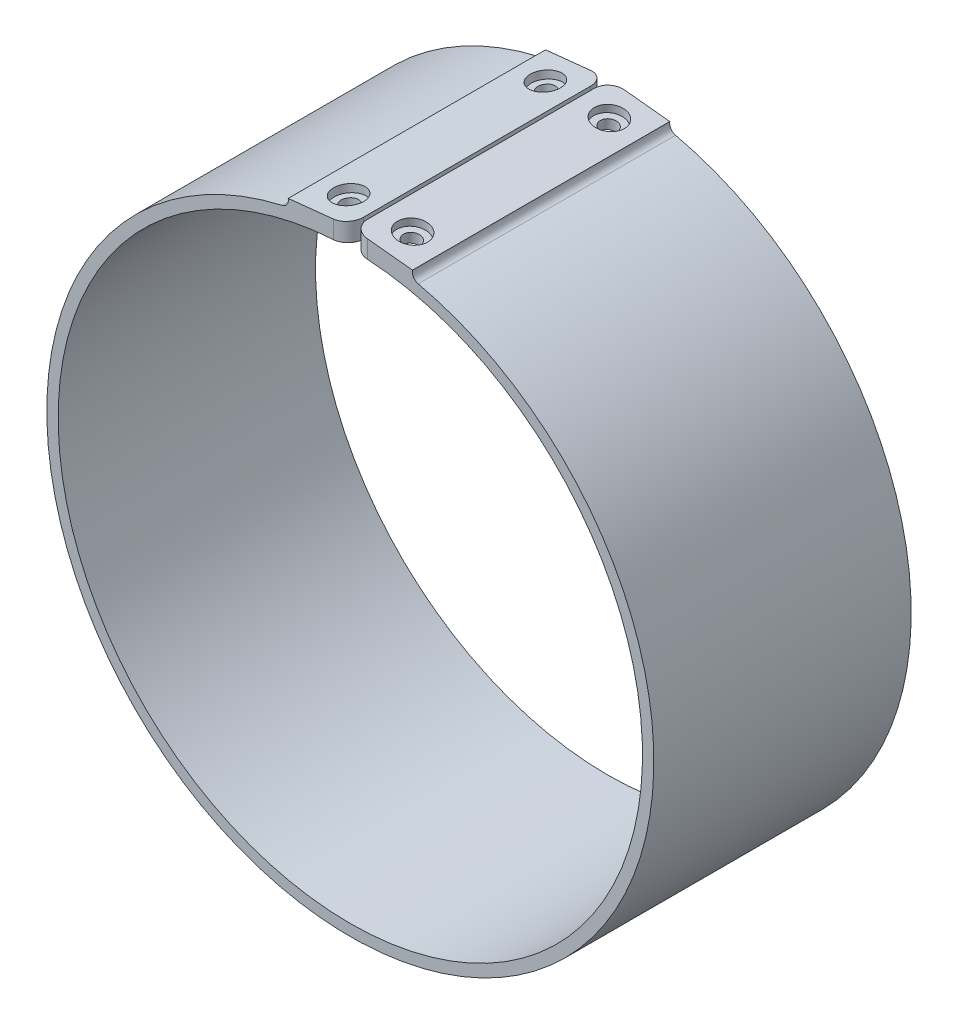
SolidWorks part; units mm, degrees
ref_plane "Front Plane" through (0, 0, 0) normal (0, 0, 1) x (1, 0, 0)
ref_plane "Top Plane" through (0, 0, 0) normal (0, 1, 0) x (1, 0, 0)
ref_plane "Right Plane" through (0, 0, 0) normal (1, 0, 0) x (0, 0, -1)
sketch "Sketch1" plane through (0, 0, 0) normal (0, 0, 1) x (1, 0, 0)
  line L0 (0, 0) -> (0, 40.1) construction
  line L2 (0.25, 38.5992) -> (0.25, 41.0992)
  line L4 (-0.25, 38.5992) -> (-0.25, 41.0992)
  line L5 (8.2071, 40.2722) -> (0.25, 41.0992)
  line L6 (-0.25, 41.0992) -> (-8.2071, 40.2722)
  line L7 (-8.2071, 40.2722) -> (-8.7003, 42.6921) construction
  arc A0 (-8.9726, 39.0833) -> (8.9726, 39.0833) centre (0, 0) ccw
  arc A1 (-0.25, 38.5992) -> (0.25, 38.5992) centre (0, 0) ccw
  arc A4 (8.2071, 40.2722) -> (8.9726, 39.0833) centre (9.1992, 40.07) ccw
  arc A5 (-8.2071, 40.2722) -> (-8.9726, 39.0833) centre (-9.1992, 40.07) cw
  circle A8 centre (0, 0) radius 40.9048 construction
  point P5 (-4.2286, 40.6857)
  point P7 (-3.2474, 43.3231)
  point P9 (-0.25, 40.9495)
  dimension "D1" = 1.5
  dimension "D2" = 77.2
  dimension "D3" = 0.5
  dimension "D4" = 8
  dimension "D5" = 2.5
extrude "Boss-Extrude1" add sketch "Sketch1" along normal blind 34
sketch "Sketch3" plane through (-4.2286, 40.6857, 0) normal (-0.1034, 0.9946, 0) x (0.9946, 0.1034, 0)
  line L0 (-4, -4) -> (4, -4) construction
  line L1 (-4, -34) -> (-4, 0) construction
  line L2 (4, -34) -> (4, 0) construction
  line L3 (4, 0) -> (-4, 0) construction
  line L4 (4, -17) -> (-4, -17) construction
  circle A0 centre (0, -4) radius 1.1
  circle A1 centre (0, -30) radius 1.1
  point P8 (0, -4)
  dimension "D1" = 2.2
  dimension "D2" = 4
extrude "Cut-Extrude2" cut sketch "Sketch3" against normal up to next
sketch "Sketch4" plane through (-4.2286, 40.6857, 0) normal (-0.1034, 0.9946, 0) x (0.9946, 0.1034, 0)
  circle A0 centre (0, -4) radius 2
  circle A1 centre (0, -30) radius 2
  dimension "D1" = 4
extrude "Cut-Extrude3" cut sketch "Sketch4" against normal blind 1
mirror "Mirror3" about plane through (0, 0, 0) normal (1, 0, 0) of "Cut-Extrude3", "Cut-Extrude2"
fillet "Fillet1" radius 2 4 edges at (-0.25, 39.8492, 0) (-0.25, 39.8492, 34) (0.25, 39.8492, 0) (0.25, 39.8492, 34)
